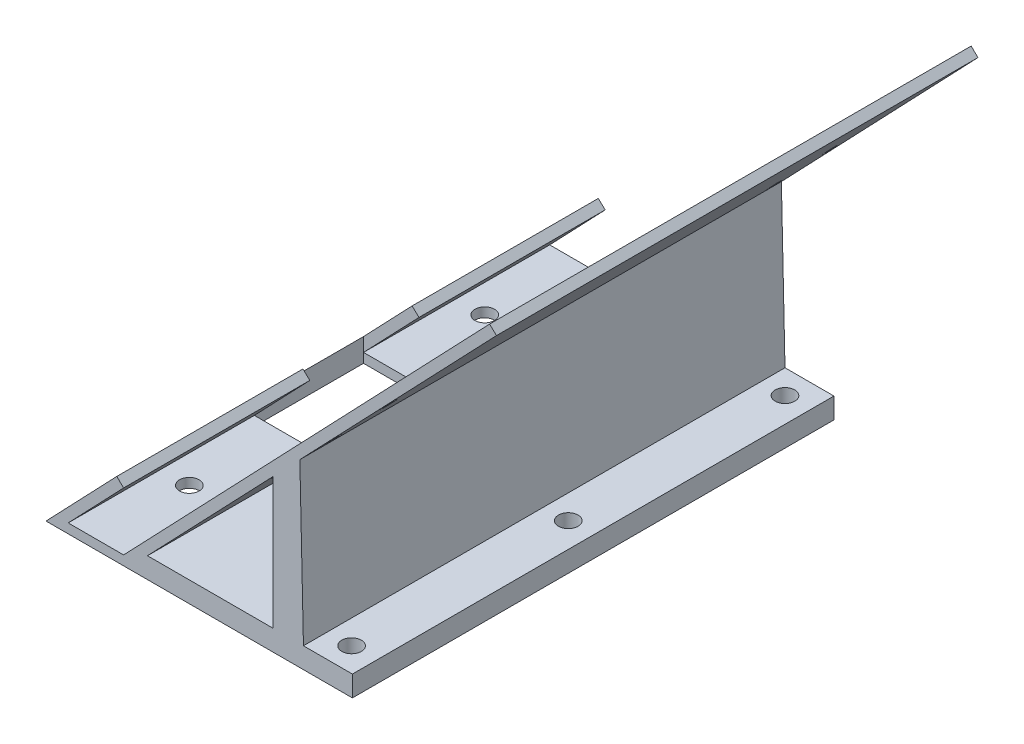
SolidWorks part; units mm, degrees
ref_plane "Front Plane" through (0, 0, 0) normal (0, 0, 1) x (1, 0, 0)
ref_plane "Top Plane" through (0, 0, 0) normal (0, 1, 0) x (1, 0, 0)
ref_plane "Right Plane" through (0, 0, 0) normal (1, 0, 0) x (0, 0, -1)
sketch "Sketch1" plane through (0, 0, 0) normal (0, 0, 1) x (1, 0, 0)
  line L0 (0, 0) -> (-8.7749, -9.181)
  line L1 (-8.7749, -9.181) -> (0, -9.181)
  line L2 (0, -9.181) -> (57.9142, 51.4138)
  line L3 (-1.0844, 1.0364) -> (-12.2834, -10.681)
  line L4 (-12.2834, -10.681) -> (0.6413, -10.681)
  line L5 (0, 50.4904) -> (0, -42.2577) construction
  line L6 (-43.3309, 0) -> (36.2013, 0) construction
  line L7 (0.6413, -10.681) -> (58.9986, 50.3774)
  line L8 (-1.0844, 1.0364) -> (0, 0)
  line L9 (57.9142, 51.4138) -> (58.9986, 50.3774)
  line L10 (0.6413, -10.681) -> (36.2013, -10.681)
  line L11 (36.2013, -10.681) -> (36.2013, -7.4044)
  line L12 (36.2013, -7.4044) -> (3.7729, -7.4044)
  line L13 (3.7729, -7.4044) -> (0.6413, -10.681)
  dimension "D1" = 83.82
  dimension "D2" = 8.7749
  dimension "D3" = 12.7
  dimension "D5" = 3.2766
  dimension "D6" = 35.56
  dimension "D4" = 1.5
extrude "Boss-Extrude1" add sketch "Sketch1" along normal blind 76.2 contours L11 L12 L7 L10 | L9 L2 L1 L0 L8 L3 L4 L7
sketch "Sketch3" plane through (0, -9.181, 0) normal (0, 1, 0) x (1, 0, 0)
  line L0 (0, -76.2) -> (0, -38.1) construction
  line L1 (0, -76.2) -> (0, 0) construction
  line L2 (0, -38.1) -> (-22.5475, -38.1) construction
  line L3 (0, -46.736) -> (-9.525, -46.736)
  line L4 (0, -38.1) -> (-9.525, -38.1)
  line L5 (0, -46.736) -> (0, -29.464)
  line L6 (0, -29.464) -> (-9.525, -29.464)
  line L7 (-9.525, -46.736) -> (-9.525, -29.464)
  line M8 (-8.7749, 0) -> (-8.7749, -76.2)
  line M10 (0, -76.2) -> (0, 0)
  dimension "D1" = 8.636
  dimension "D2" = 9.525
extrude "Cut-Extrude1" cut sketch "Sketch3" along normal mid plane 66.04 contours L4 L3 M10 M8 | L6 L4 M10 M8
sketch "Sketch5" plane through (4.5858, -4.383, 0) normal (-0.7229, 0.6909, 0) x (0, 0, 1)
  line L0 (0, 35.2729) -> (76.2, 35.2729) construction
  line L1 (0, -6.6371) -> (0, 77.1829) construction
  line L2 (76.2, -6.6371) -> (76.2, 77.1829) construction
  line L3 (38.1, 77.1829) -> (38.1, -6.6371) construction
  line L4 (76.2, 77.1829) -> (0, 77.1829) construction
  line L5 (29.464, -6.6371) -> (46.736, -6.6371) construction
  line L6 (2.54, 23.8429) -> (2.54, 21.3029)
  line L7 (2.54, 36.5429) -> (3.81, 36.5429)
  line L8 (2.54, 36.5429) -> (2.54, 34.0029)
  line L9 (2.54, 34.0029) -> (3.81, 34.0029)
  line L10 (3.81, 36.5429) -> (3.81, 34.0029)
  line L11 (2.54, 36.5429) -> (3.81, 34.0029) construction
  line L12 (2.54, 34.0029) -> (3.81, 36.5429) construction
  line L13 (2.54, 23.8429) -> (3.81, 23.8429)
  line L14 (3.81, 23.8429) -> (3.81, 21.3029)
  line L15 (2.54, 21.3029) -> (3.81, 21.3029)
  line L16 (2.54, 49.2429) -> (2.54, 46.7029)
  line L17 (2.54, 49.2429) -> (3.81, 49.2429)
  line L18 (3.81, 49.2429) -> (3.81, 46.7029)
  line L19 (2.54, 46.7029) -> (3.81, 46.7029)
  line L20 (73.66, 23.8429) -> (72.39, 23.8429)
  line L21 (72.39, 23.8429) -> (72.39, 21.3029)
  line L22 (73.66, 21.3029) -> (72.39, 21.3029)
  line L23 (73.66, 23.8429) -> (73.66, 21.3029)
  line L24 (73.66, 34.0029) -> (72.39, 34.0029)
  line L25 (72.39, 36.5429) -> (72.39, 34.0029)
  line L26 (73.66, 36.5429) -> (72.39, 36.5429)
  line L27 (73.66, 36.5429) -> (73.66, 34.0029)
  line L28 (73.66, 49.2429) -> (72.39, 49.2429)
  line L29 (72.39, 49.2429) -> (72.39, 46.7029)
  line L30 (73.66, 46.7029) -> (72.39, 46.7029)
  line L31 (73.66, 49.2429) -> (73.66, 46.7029)
  point P12 (3.175, 35.2729)
  dimension "D1" = 2.54
  dimension "D2" = 2.54
  dimension "D3" = 1.27
  dimension "D4" = 2
  dimension "D5" = 2
extrude "Cut-Extrude2" cut sketch "Sketch5" against normal up to surface (1.5 mm away) up to face at (31.3858, 21.4865, 38.1)
sketch "Sketch6" plane through (0, 0, 76.2) normal (0, 0, 1) x (1, 0, 0)
  line L0 (23.6282, -7.4044) -> (23.6282, 13.3698)
  line L1 (36.2013, -7.4044) -> (3.7729, -7.4044) construction
  line L2 (3.7729, -7.4044) -> (58.9986, 50.3774) construction
  line L3 (23.6282, 13.3698) -> (27.8851, 17.8238)
  line L4 (27.8851, 17.8238) -> (28.4557, -7.4044)
  line L5 (28.4557, -7.4044) -> (23.6282, -7.4044)
extrude "Boss-Extrude2" add sketch "Sketch6" against normal up to surface (76.2 mm away) up to face at (17.0946, 4.8295, 0)
sketch "Sketch7" plane through (0, -7.4044, 0) normal (0, 1, 0) x (1, 0, 0)
  line L0 (28.4557, 0) -> (28.4557, -76.2) construction
  line L1 (36.2013, -76.2) -> (28.4557, -76.2) construction
  line L2 (36.2013, 0) -> (28.4557, 0) construction
  circle A0 centre (32.2657, -72.39) radius 1.55
  circle A1 centre (32.2657, -3.81) radius 1.55
  circle A2 centre (32.2657, -38.1) radius 1.55
  dimension "D1" = 3.1
  dimension "D2" = 3.1
  dimension "D8" = 3.1
  dimension "D3" = 3.81
  dimension "D4" = 3.81
  dimension "D5" = 3.81
  dimension "D6" = 3.81
  dimension "D7" = 34.29
  dimension "D9" = 3.81
extrude "Cut-Extrude3" cut sketch "Sketch7" against normal up to surface (3.2766 mm away) up to face at (11.9589, -10.681, 38.1)
sketch "Sketch9" plane through (0, -9.181, 0) normal (0, 1, 0) x (1, 0, 0)
  line L0 (-8.7749, -76.2) -> (0, -76.2) construction
  line L1 (-8.7749, -76.2) -> (-8.7749, -46.736) construction
  line L2 (0, -38.1) -> (-26.97, -38.1) construction
  line L3 (0, -29.464) -> (0, -46.736) construction
  circle A0 centre (-4.3299, -61.468) radius 1.55
  circle A1 centre (-4.3299, -14.732) radius 1.55
  dimension "D2" = 3.1
  dimension "D1" = 14.732
  dimension "D3" = 4.445
extrude "Cut-Extrude4" cut sketch "Sketch9" against normal up to surface (1.5 mm away) up to face at (32.2657, -10.681, 73.94)
